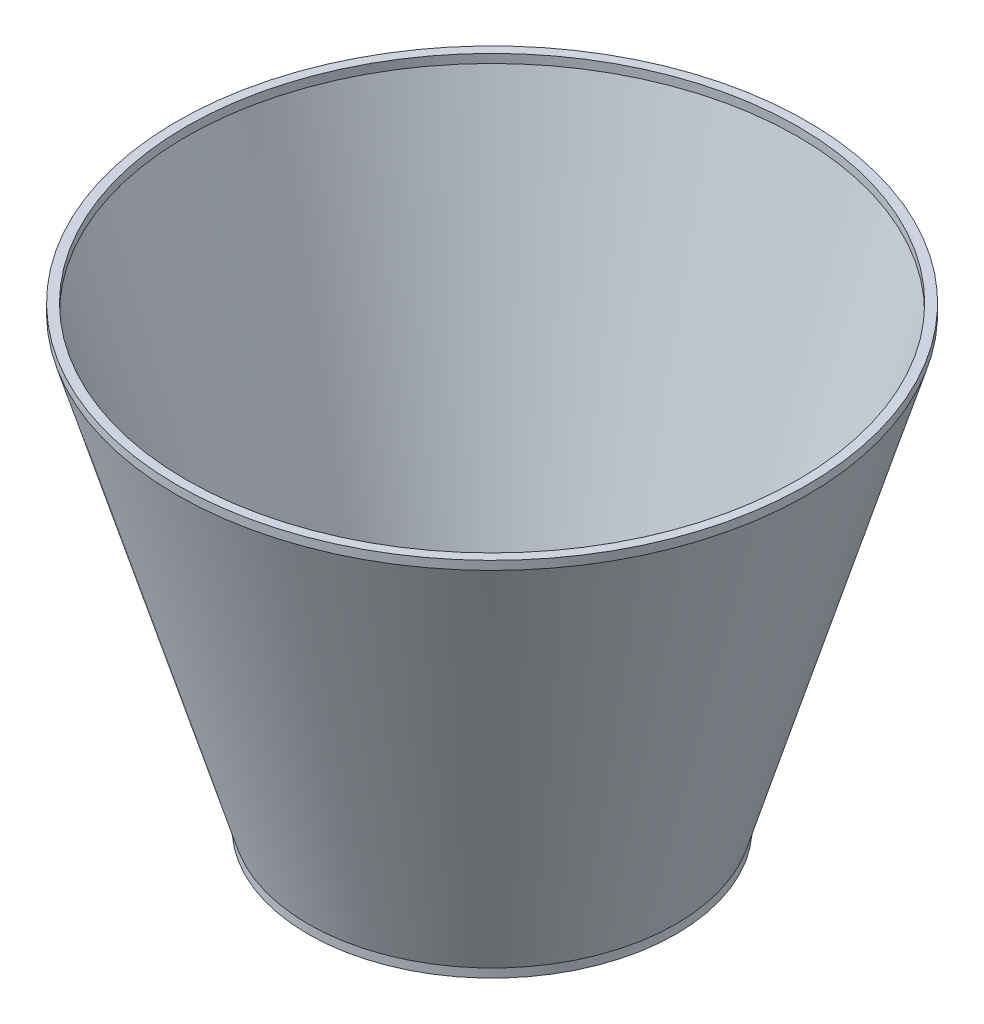
SolidWorks part; units mm, degrees
ref_plane "Front Plane" through (0, 0, 0) normal (0, 0, 1) x (1, 0, 0)
ref_plane "Top Plane" through (0, 0, 0) normal (0, 1, 0) x (1, 0, 0)
ref_plane "Right Plane" through (0, 0, 0) normal (1, 0, 0) x (0, 0, -1)
sketch "Sketch1" plane through (0, 0, 0) normal (0, 0, 1) x (1, 0, 0)
  line L0 (-40, 0) -> (-70, 100)
  line L1 (0, 0) -> (0, 68.8325) construction
  line L2 (-42.0881, 0) -> (-72.0881, 100)
  line L3 (-70, 100) -> (-72.0881, 100)
  line L4 (-40, 0) -> (-42.0881, 0)
  line L5 (-41.9157, -0.5747) -> (-71.9157, 99.4253) construction
  dimension "D1" = 40
  dimension "D2" = 70
  dimension "D3" = 100
  dimension "D4" = 0
  dimension "D5" = 2
revolve "Revolve1" add sketch "Sketch1" angle 360 about L1
sketch "Sketch2" plane through (0, 0, 0) normal (0, -1, 0) x (1, 0, 0)
  circle A0 centre (0, 0) radius 42.0881
  circle A1 centre (0, 0) radius 40
  circle A2 centre (0, 0) radius 40 construction
  circle A4 centre (0, 0) radius 42.0881 construction
  dimension "D1" = 0
  dimension "D2" = 0
extrude "Boss-Extrude1" add sketch "Sketch2" along normal blind 2
sketch "Sketch3" plane through (0, 100, 0) normal (0, 1, 0) x (1, 0, 0)
  circle A0 centre (0, 0) radius 70
  circle A1 centre (0, 0) radius 72.0881
  circle A2 centre (0, 0) radius 72.0881 construction
  circle A3 centre (0, 0) radius 70 construction
  dimension "D1" = 0
  dimension "D2" = 0
extrude "Boss-Extrude2" add sketch "Sketch3" along normal blind 2
